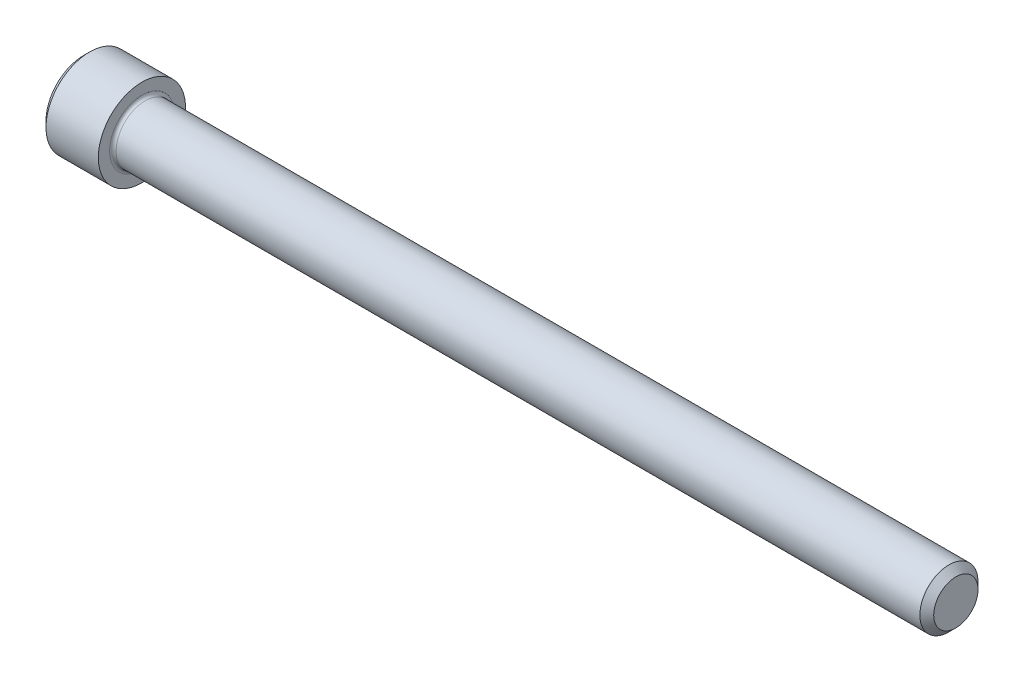
SolidWorks part; units mm, degrees
revolve "Base-Revolve" add sketch "BodySke"
sketch "BodySke" plane through (0, 0, 0) normal (0, 0, 1) x (1, 0, 0)
  line L0 (0, 0) -> (0, 4.1275)
  line L1 (0.635, 4.7625) -> (6.35, 4.7625)
  line L2 (6.35, 4.7625) -> (6.35, 3.175)
  line L3 (6.35, 3.175) -> (94.4943, 3.175)
  line L4 (95.25, 2.4193) -> (95.25, 0)
  line L5 (95.25, 0) -> (0, 0)
  line L6 (-31.75, 0) -> (127, 0) construction
  line L7 (0, 4.1275) -> (0.635, 4.7625)
  line L8 (95.25, 2.4193) -> (94.4943, 3.175)
  line L9 (0, -4.1275) -> (0.635, -4.7625) construction
  line L10 (95.25, -2.4193) -> (94.4943, -3.175) construction
  line L11 (7.62, 9.525) -> (7.62, 3.175) construction
  line L12 (69.85, 9.525) -> (69.85, 3.175) construction
  line L13 (57.15, 9.525) -> (57.15, 3.175) construction
  dimension "Diameter" = 6.35
  dimension "Head_ht" = 6.35
  dimension "Length" = 88.9
  dimension "Body_ch_ang" = 45
  dimension "Head_dia" = 9.525
  dimension "Head_ch_ang" = 45
  dimension "Head_side_ht" = 5.715
  dimension "Minor_dia" = 4.8387
  dimension "Advance" = 1.27
  dimension "Thread_nom" = 25.4
  dimension "Thread_length" = 38.1
cosmetic thread "ThreadCosmetic"
fillet "Fillet1" radius 0.3556 1 edges at (6.35, 0, 3.175)
ref_plane "Plane1" through (0, 0, 0) normal (0, 0, 1) x (1, 0, 0)
ref_plane "Plane2" through (0, 0, 0) normal (0, 1, 0) x (1, 0, 0)
ref_plane "Plane3" through (0, 0, 0) normal (1, 0, 0) x (0, 0, -1)
sketch "Sketch2" plane through (0, 0, 0) normal (0, 0, 1) x (1, 0, 0)
  line L0 (0, 2.3813) -> (3.048, 2.3813)
  line L1 (3.048, 2.3813) -> (4.4228, 0)
  line L2 (-31.75, 0) -> (127, 0) construction
  line L3 (4.4228, 0) -> (0, 0)
  line L4 (0, 0) -> (0, 2.3813)
  line L5 (0, 4.1275) -> (0, -4.1275) construction
  line L6 (0, 0) -> (47.625, 0) construction
  line L7 (6.35, -4.7625) -> (6.35, 4.7625) construction
  dimension "D1" = 2.3813
  dimension "D2" = 60
revolve "Hex-PreBroach" cut sketch "Sketch2" angle 360 about L6
sketch "Sketch3" plane through (0, 0, 0) normal (-1, 0, 0) x (0, 0.5, 0.866)
  line L0 (1.3748, 2.3813) -> (-1.3748, 2.3813)
  line L1 (-1.3748, 2.3813) -> (-2.7496, 0)
  line L2 (1.3748, 2.3813) -> (2.7496, 0)
  line L3 (1.3748, -2.3812) -> (2.7496, 0)
  line L4 (1.3748, -2.3812) -> (-1.3748, -2.3812)
  line L5 (-1.3748, -2.3812) -> (-2.7496, 0)
  dimension "D1" = 2.3813
  dimension "D2" = 2.3813
  dimension "Hex_size" = 4.7625
extrude "Hex" cut sketch "Sketch3" against normal blind 3.048
sketch "Sketch4" plane through (0, 0, 0) normal (-1, 0, 0) x (0, 0, 1)
  line L0 (0, 0) -> (2.8067, 0)
  line L1 (0, 0) -> (6.1484, 3.5498) construction
  line L2 (0, 0) -> (1.4033, 2.4307)
  line L3 (2.3336, 0.614) -> (2.6851, 0.817)
  line L4 (1.6986, 1.7139) -> (2.0501, 1.9169)
  arc A0 (2.3336, 0.614) -> (1.6986, 1.7139) centre (0, 0) ccw
  arc A1 (2.8067, 0) -> (2.6851, 0.817) centre (0, 0) ccw
  arc A2 (1.4033, 2.4307) -> (2.0501, 1.9169) centre (0, 0) cw
  dimension "D1" = 30
  dimension "D2" = 60
  dimension "Spline_p_dim" = 1.27
  dimension "D3" = 0.635
extrude "Spline" [suppressed] cut sketch "Sketch4" against normal blind 3.048
pattern_circular "CirPattern1" [suppressed] count 6 every 60
sketch "Sketch5" plane through (0, 0, 0) normal (0, 0, 1) x (1, 0, 0)
  line L0 (-31.75, 0) -> (127, 0) construction
  line L2 (0, 4.1275) -> (0, -4.1275) construction
  circle A0 centre (2.159, 0) radius 0.5905
  dimension "Drilled_hole_dia" = 1.1811
  dimension "Drilled_hole_loc" = 2.159
extrude "Hole" [suppressed] cut sketch "Sketch5" against normal through all and the other way through all
pattern_circular "Drilled-4" [suppressed] count 2 every 60
pattern_circular "Drilled-6" [suppressed] count 3 every 60
sketch "ThdSchSke" plane through (0, 0, 0) normal (0, 0, 1) x (1, 0, 0)
  line L0 (69.85, -2.4193) -> (69.3209, -3.175)
  line L1 (69.85, -2.4193) -> (70.3791, -3.175)
  line L2 (70.3791, -3.175) -> (70.3791, -3.9687)
  line L3 (-3.175, 0) -> (5.1513, 0) construction
  line L5 (70.3791, -3.9687) -> (69.3209, -3.9687)
  line L6 (69.3209, -3.9687) -> (69.3209, -3.175)
  line L7 (0, 4.1275) -> (0, -4.1275) construction
  dimension "Thread_minor" = 4.8387
  dimension "Diameter" = 6.35
  dimension "Start" = 69.85
revolve "ThreadSchematic" [suppressed] cut sketch "ThdSchSke" angle 360 about L3
pattern_linear "ThdSchPat" [suppressed]
equation "\"D2@Sketch3\" = \"Hex_size@Sketch3\" / 2"
equation "\"D1@Sketch3\" = \"Hex_size@Sketch3\" / 2"
equation "\"D1@Sketch2\" = \"Hex_size@Sketch3\" / 2"
equation "\"D3@Sketch4\" = \"Spline_p_dim@Sketch4\" / 2"
equation "\"Thread_minor@ThreadCosmetic\"  =  \"Minor_dia@BodySke\""
equation "\"D2@CirPattern1\" = 360 / \"Num_teeth@CirPattern1\""
equation "\"Wall_thickness@Sketch2\" = \"Head_ht@BodySke\" - \"Key_eng@Hex\""
equation "\"Thread_length@ThreadCosmetic\" = ((sgn( (\"Length@BodySke\" - \"Advance@BodySke\" ) - \"Thread_nom@BodySke\" )-1)*( (\"Length@BodySke\" - \"Advance@BodySke\" ) - \"Thread_nom@BodySke\" ))/-2+ \"Thread_nom@BodySke\""
equation "\"Thread_minor@ThdSchSke\" = \"Minor_dia@BodySke\""
equation "\"Diameter@ThdSchSke\" = \"Diameter@BodySke\""
equation "\"Overcut@ThdSchSke\" = \"Diameter@BodySke\" * 1.25"
equation "\"Start@ThdSchSke\" = \"Head_ht@BodySke\" + \"Length@BodySke\" - \"Thread_length@ThreadCosmetic\"  '---Non-countersunk---"
equation "\"Num_threads@ThdSchPat\" = int( \"Thread_length@ThreadCosmetic\" / \"Advance@BodySke\" + 0.999 )  + 1"
equation "\"Advance@ThdSchPat\" = \"Thread_length@ThreadCosmetic\" /  (\"Num_threads@ThdSchPat\" - 1) 'relax it"
equation "\"Num_threads@ThdSchPat\" = \"Num_threads@ThdSchPat\" - sgn( \"Num_threads@ThdSchPat\" - 1) '---chamfered tips only---"
